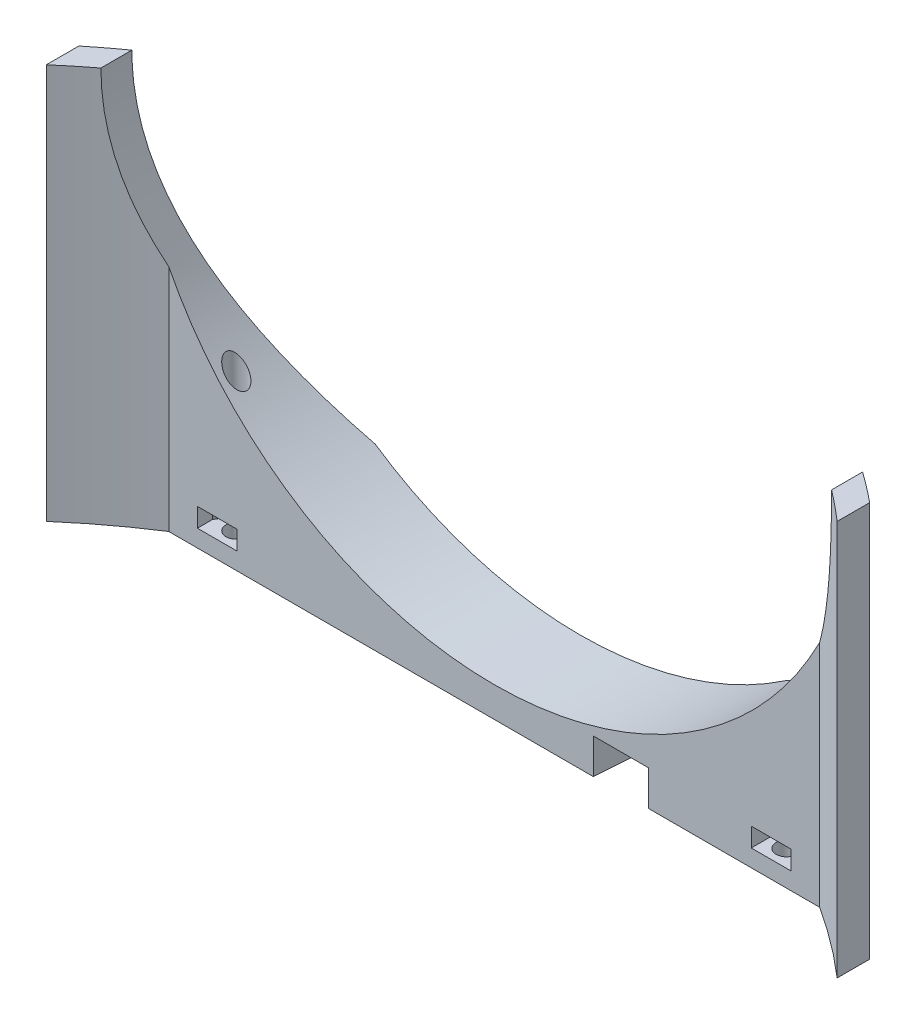
SolidWorks part; units mm, degrees
ref_plane "Front Plane" through (0, 0, 0) normal (0, 0, 1) x (1, 0, 0)
ref_plane "Top Plane" through (0, 0, 0) normal (0, 1, 0) x (1, 0, 0)
ref_plane "Right Plane" through (0, 0, 0) normal (1, 0, 0) x (0, 0, -1)
sketch "Sketch1" plane through (0, 0, 0) normal (0, 1, 0) x (1, 0, 0)
  line L1 (-46, 15.5) -> (46, 15.5)
  line L2 (-46, 15.5) -> (-46, -15.5)
  line L3 (-46, -15.5) -> (46, -15.5)
  line L4 (46, 15.5) -> (46, -15.5)
  line L5 (-46, 15.5) -> (46, -15.5) construction
  line L6 (-46, -15.5) -> (46, 15.5) construction
  point P0 (0, 0)
  dimension "D1" = 31
  dimension "D2" = 92
extrude "Boss-Extrude1" add sketch "Sketch1" along normal blind 46
sketch "Sketch2" plane through (0, 46, 0) normal (0, 1, 0) x (1, 0, 0)
  line L0 (-46, -15.5) -> (46, -15.5) construction
  circle A0 centre (0, -53.5) radius 73
  circle A1 centre (0, -53.5) radius 103
  dimension "D2" = 146
  dimension "D3" = 30
  dimension "D1" = 38
extrude "Cut-Extrude1" cut sketch "Sketch2" against normal through all
sketch "Sketch7" plane through (0, 0, 0) normal (0, -1, 0) x (1, 0, 0)
  line L0 (-46, 15.5) -> (46, 15.5) construction
  line L1 (-46, -3.1833) -> (-46, 15.5) construction
  line L2 (46, 15.5) -> (46, -3.1833) construction
  circle A0 centre (-32, -7.5) radius 1.2
  circle A1 centre (32, -7.5) radius 1.2
  dimension "D5" = 2.4
  dimension "D6" = 2.4
  dimension "D1" = 23
  dimension "D2" = 14
  dimension "D3" = 23
  dimension "D4" = 14
extrude "Cut-Extrude5" cut sketch "Sketch7" against normal through all
sketch "Sketch3" plane through (0, 46, 0) normal (0, 1, 0) x (1, 0, 0)
  line L0 (-46, -15.5) -> (46, -15.5) construction
  line L1 (-37.8551, 5.5) -> (37.8551, 5.5)
  arc A0 (-37.8551, 5.5) -> (37.8551, 5.5) centre (0, -53.5) ccw
  dimension "D1" = 70.1
  dimension "D2" = 38
  dimension "D3" = 59
extrude "Cut-Extrude2" cut sketch "Sketch3" against normal through all
sketch "Sketch5" plane through (0, 0, -15.5) normal (0, 0, -1) x (-1, 0, 0)
  line L0 (-23.8328, 46) -> (23.8328, 46) construction
  circle A0 centre (0, 46) radius 42.5
  dimension "D1" = 85
extrude "Cut-Extrude4" cut sketch "Sketch5" against normal through all
sketch "Sketch8" plane through (0, 0, 0) normal (0, -1, 0) x (1, 0, 0)
  line L4 (-34.5236, -7.2291) -> (-33.1836, -9.55)
  line L5 (-33.1836, -9.55) -> (-30.8164, -9.55)
  line L6 (-30.8164, -9.55) -> (-29.9048, -7.9709)
  line L7 (0, -5.5) -> (0, -15.5) construction
  line L10 (-34.5236, -7.2291) -> (-34.5236, -4.9723)
  line L11 (-33.9919, -6.85) -> (-34.5692, -7.85)
  line L12 (-29.6929, -7.3959) -> (-30.2703, -6.3959)
  line L13 (-30.9366, -5.45) -> (-33.246, -5.45)
  line L14 (-34.5236, -4.9723) -> (-29.9048, -4.9723)
  line L15 (-29.9048, -4.9723) -> (-29.9048, -7.9709)
  line L16 (37.8551, -5.5) -> (-37.8551, -5.5) construction
  line L17 (23.8328, -15.5) -> (-23.8328, -15.5) construction
  line L18 (29.9048, -4.9723) -> (29.9048, -7.9709)
  line L19 (34.5236, -4.9723) -> (29.9048, -4.9723)
  line L20 (34.5236, -7.2291) -> (34.5236, -4.9723)
  line L21 (30.8164, -9.55) -> (29.9048, -7.9709)
  line L22 (33.1836, -9.55) -> (30.8164, -9.55)
  line L23 (34.5236, -7.2291) -> (33.1836, -9.55)
  arc A0 (-33.5132, -8.9791) -> (-29.9625, -8.0709) centre (-32, -7.5) ccw construction
  arc A1 (33.5132, -8.9791) -> (29.9625, -8.0709) centre (32, -7.5) cw construction
  dimension "D1" = 4.6188
  dimension "D2" = 2.05
extrude "Cut-Extrude6" cut sketch "Sketch8" against normal blind 2.2 from offset 2 offset against normal yes
sketch "Sketch9" plane through (0, 0, -15.5) normal (0, 0, -1) x (-1, 0, 0)
  line L2 (-23.8328, 0) -> (23.8328, 0) construction
  line L3 (-17.2328, 0) -> (-12.2328, 0)
  line L4 (-17.2328, 0) -> (-17.2328, 3.4)
  line L5 (-17.2328, 3.4) -> (-12.2328, 3.4)
  line L6 (-12.2328, 0) -> (-12.2328, 3.4)
  line L7 (-23.8328, 0) -> (-23.8328, 10.8112) construction
  dimension "D1" = 5
  dimension "D2" = 6.6
  dimension "D3" = 3.4
extrude "Cut-Extrude7" cut sketch "Sketch9" against normal through all draft 4 draft outward yes
